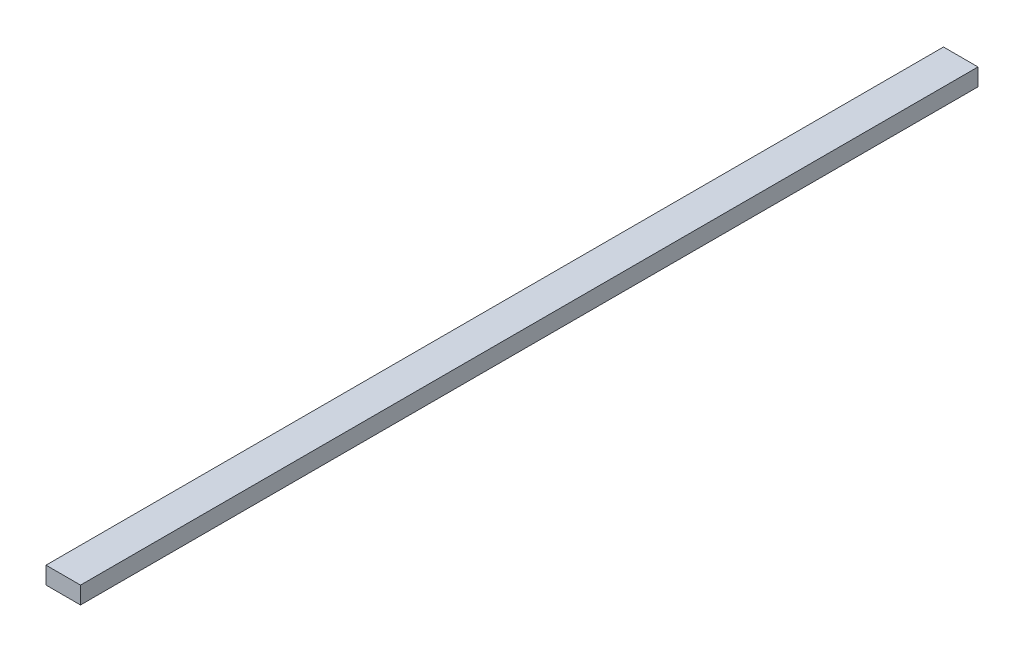
SolidWorks part; units mm, degrees
ref_plane "Front" through (0, 0, 0) normal (0, 0, 1) x (1, 0, 0)
ref_plane "Top" through (0, 0, 0) normal (0, 1, 0) x (1, 0, 0)
ref_plane "Right" through (0, 0, 0) normal (1, 0, 0) x (0, 0, -1)
sketch "Эскиз1" plane through (0, 0, 0) normal (0, 0, 1) x (1, 0, 0)
  line L1 (-23.9098, 22.6316) -> (56.0902, 22.6316)
  line L2 (-23.9098, 22.6316) -> (-23.9098, -17.3684)
  line L3 (-23.9098, -17.3684) -> (56.0902, -17.3684)
  line L4 (56.0902, 22.6316) -> (56.0902, -17.3684)
  dimension "D1" = 40
  dimension "D2" = 80
extrude "Бобышка-Вытянуть1" add sketch "Эскиз1" along normal blind 2080
